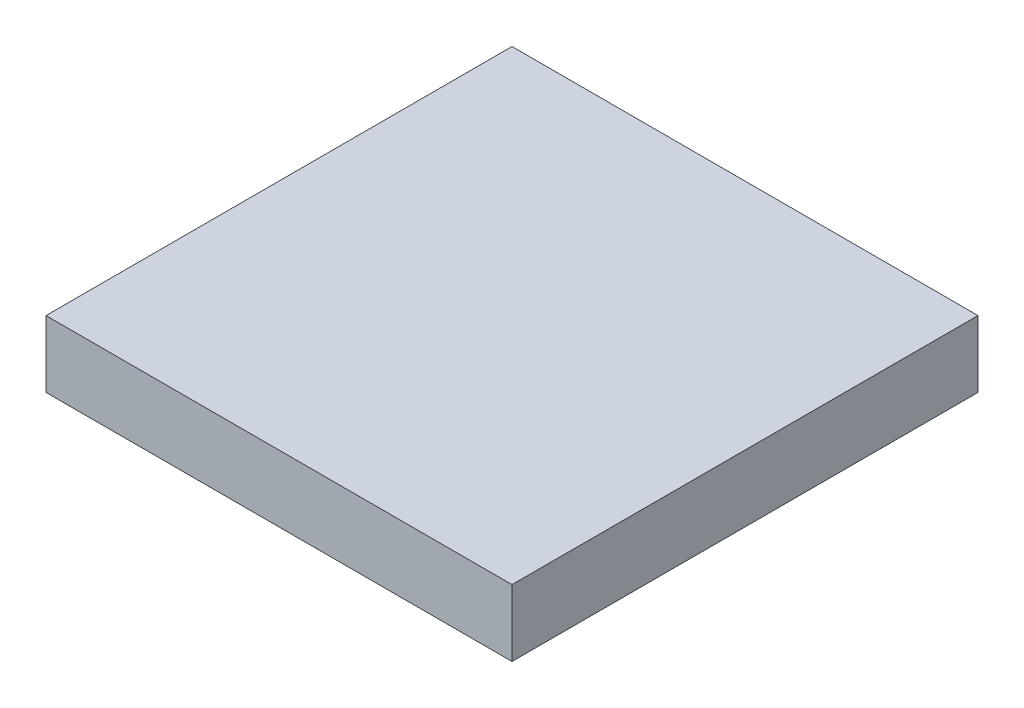
SolidWorks part; units mm, degrees
ref_plane "Front" through (0, 0, 0) normal (0, 0, 1) x (1, 0, 0)
ref_plane "Top" through (0, 0, 0) normal (0, 1, 0) x (1, 0, 0)
ref_plane "Right" through (0, 0, 0) normal (1, 0, 0) x (0, 0, -1)
sketch "草图1" plane through (0, 0, 0) normal (0, 1, 0) x (1, 0, 0)
  line L1 (-7, 7) -> (7, 7)
  line L2 (-7, 7) -> (-7, -7)
  line L3 (-7, -7) -> (7, -7)
  line L4 (7, 7) -> (7, -7)
  line L5 (-7, 7) -> (7, -7) construction
  line L6 (-7, -7) -> (7, 7) construction
  point P0 (0, 0)
  dimension "D1" = 14
extrude "凸台-拉伸1" add sketch "草图1" along normal blind 2
